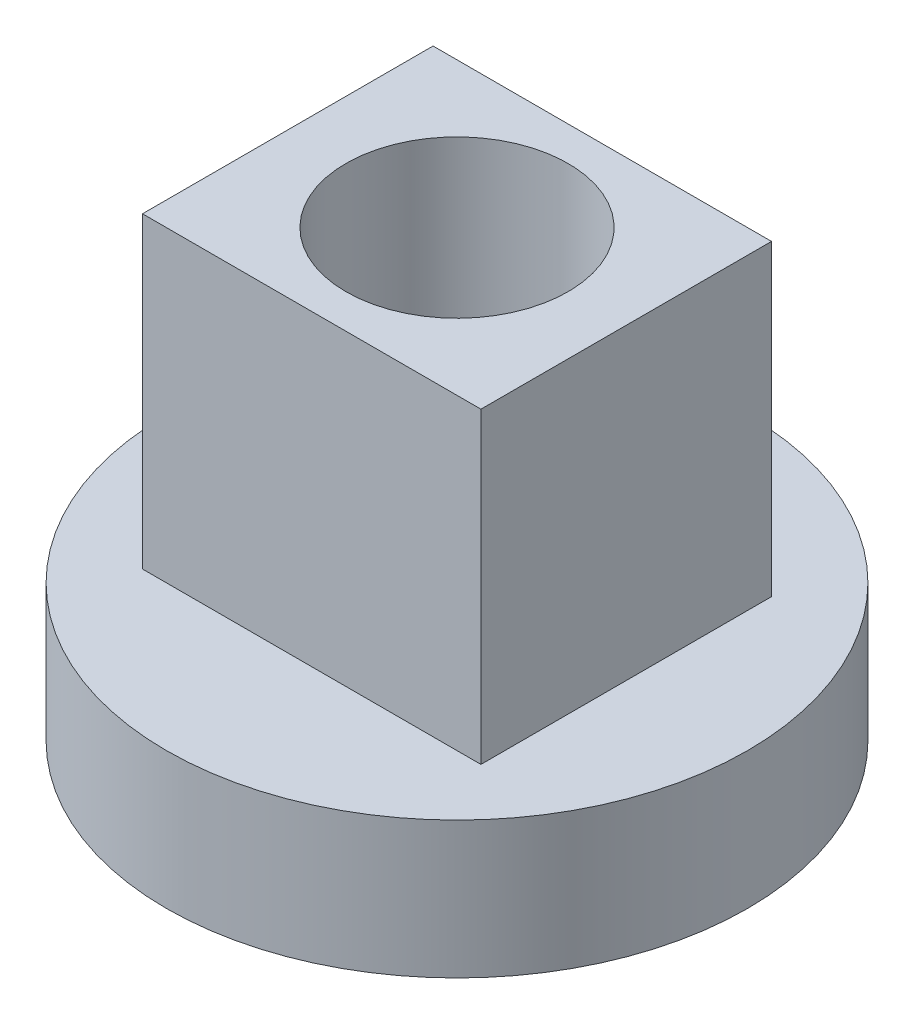
SolidWorks part; units mm, degrees
ref_plane "Front Plane" through (0, 0, 0) normal (0, 0, 1) x (1, 0, 0)
ref_plane "Top Plane" through (0, 0, 0) normal (0, 1, 0) x (1, 0, 0)
ref_plane "Right Plane" through (0, 0, 0) normal (1, 0, 0) x (0, 0, -1)
sketch "Sketch1" plane through (0, 0, 0) normal (0, 1, 0) x (1, 0, 0)
  circle A0 centre (0, 0) radius 4.318
extrude "Boss-Extrude1" add sketch "Sketch1" along normal blind 2.032
sketch "Sketch2" plane through (0, 2.032, 0) normal (0, 1, 0) x (1, 0, 0)
  line L1 (-2.5146, 2.159) -> (2.5146, 2.159)
  line L2 (-2.5146, 2.159) -> (-2.5146, -2.159)
  line L3 (-2.5146, -2.159) -> (2.5146, -2.159)
  line L4 (2.5146, 2.159) -> (2.5146, -2.159)
  line L5 (-2.5146, 2.159) -> (2.5146, -2.159) construction
  line L6 (-2.5146, -2.159) -> (2.5146, 2.159) construction
  point P0 (0, 0)
extrude "Boss-Extrude2" add sketch "Sketch2" along normal blind 4.572
sketch "Sketch3" plane through (0, 6.604, 0) normal (0, 1, 0) x (1, 0, 0)
  circle A0 centre (0, 0) radius 1.651
extrude "Cut-Extrude1" cut sketch "Sketch3" against normal through all
